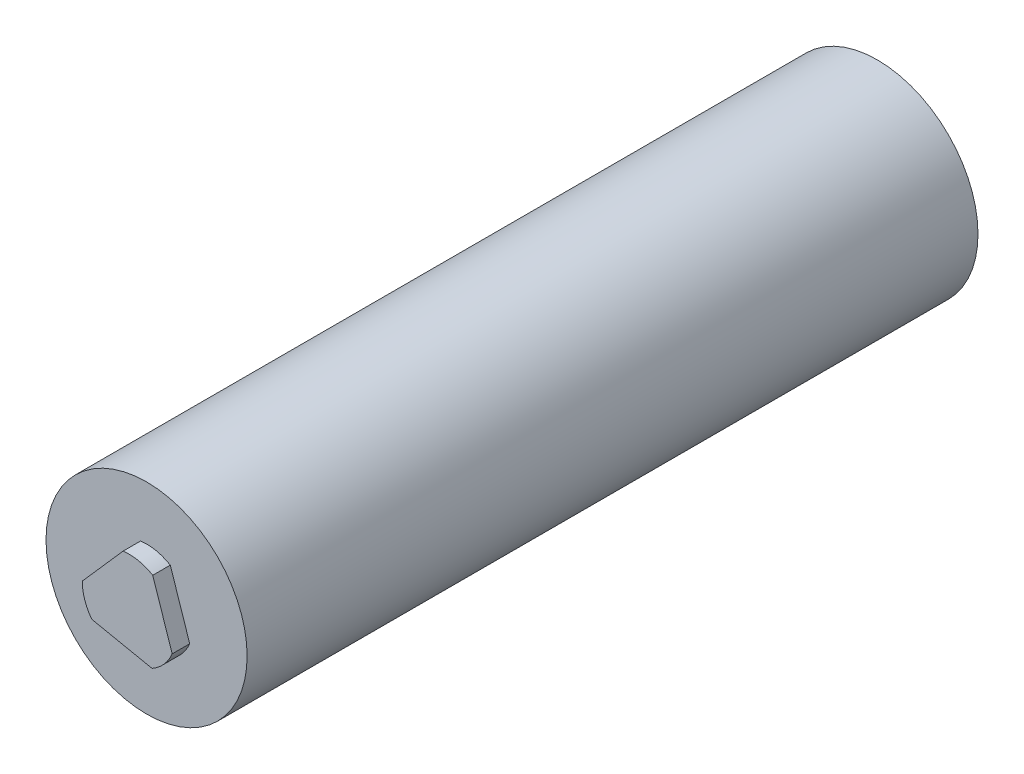
SolidWorks part; units mm, degrees
material "1.2083 (X40Cr14)"
ref_plane "Спереди" through (0, 0, 0) normal (0, 0, 1) x (1, 0, 0)
ref_plane "Сверху" through (0, 0, 0) normal (0, 1, 0) x (1, 0, 0)
ref_plane "Справа" through (0, 0, 0) normal (1, 0, 0) x (0, 0, -1)
sketch "Эскиз1" plane through (0, 0, 0) normal (0, 0, 1) x (1, 0, 0)
  circle A0 centre (0, 0) radius 8.6
extrude "Бобышка-Вытянуть1" add sketch "Эскиз1" along normal blind 64
sketch "Эскиз2" plane through (0, 0, 64) normal (0, 0, 1) x (1, 0, 0)
  line L0 (2.0282, 3.4477) -> (3.6897, -1.5447)
  line L1 (4.5069, -4.0004) -> (1.2109, 5.9033) construction
  line L2 (1.2109, 5.9033) -> (-5.7179, -1.9029) construction
  line L3 (-5.7179, -1.9029) -> (4.5069, -4.0004) construction
  line L4 (-0.5071, 3.9677) -> (-4, 0)
  line L5 (-3.1826, -2.423) -> (1.9717, -3.4803)
  circle A0 centre (0, 0) radius 4 construction
  circle A1 centre (0, 0) radius 3.0131 construction
  arc A2 (-0.5071, 3.9677) -> (2.0282, 3.4477) centre (0, 0) cw
  arc A3 (3.6897, -1.5447) -> (1.9717, -3.4803) centre (0, 0) cw
  arc A4 (-4, 0) -> (-3.1826, -2.423) centre (0, 0) ccw
  dimension "D1" = 8
extrude "Вырез-Вытянуть1" cut sketch "Эскиз2" against normal blind 1.5 flip side to cut
